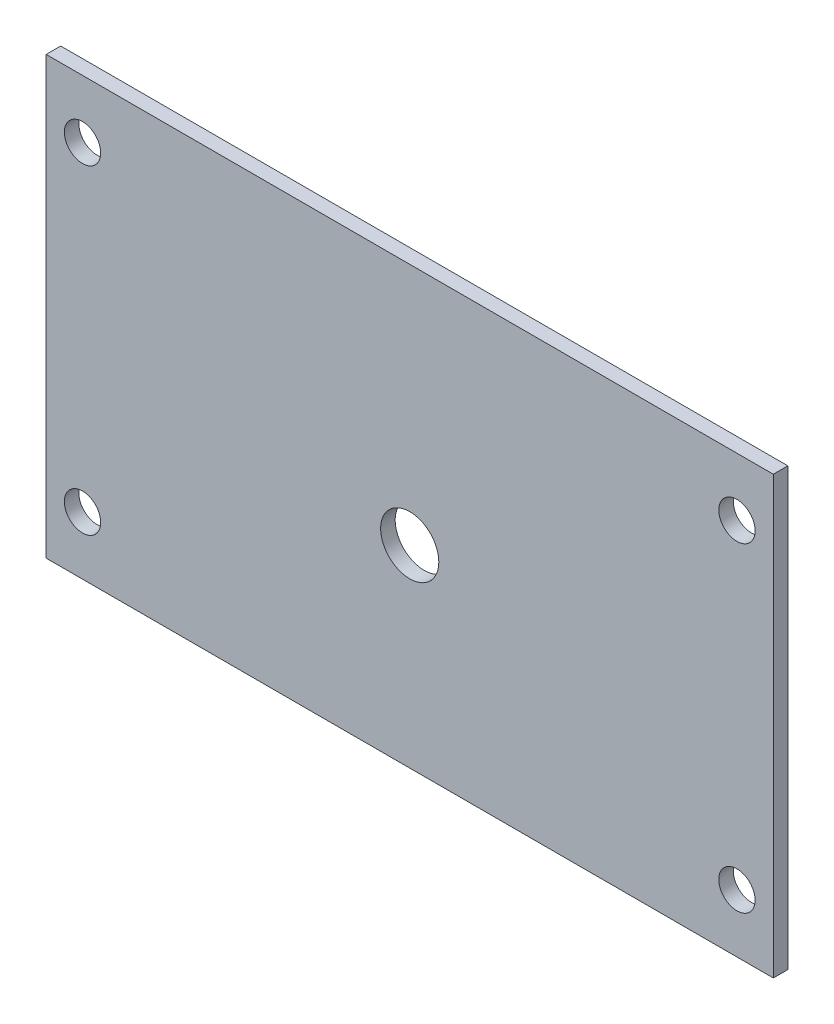
SolidWorks part; units mm, degrees
ref_plane "Front Plane" through (0, 0, 0) normal (0, 0, 1) x (1, 0, 0)
ref_plane "Top Plane" through (0, 0, 0) normal (0, 1, 0) x (1, 0, 0)
ref_plane "Right Plane" through (0, 0, 0) normal (1, 0, 0) x (0, 0, -1)
sketch "Sketch1" plane through (0, 0, 0) normal (0, 0, 1) x (1, 0, 0)
  line L0 (0, 30) -> (0, -30) construction
  line L1 (-50, -30) -> (50, -30)
  line L2 (-50, -30) -> (-50, 30)
  line L3 (-50, 30) -> (50, 30)
  line L4 (50, -30) -> (50, 30)
  line L5 (-50, -30) -> (50, 30) construction
  line L6 (-50, 30) -> (50, -30) construction
  circle A0 centre (0, -3.4588) radius 4
  circle A1 centre (-45, 22) radius 2.5
  circle A2 centre (-45, -22) radius 2.5
  circle A3 centre (45, -22) radius 2.5
  circle A4 centre (45, 22) radius 2.5
  point P0 (0, 0)
  dimension "D3" = 8
  dimension "D4" = 5
  dimension "D7" = 5
  dimension "D1" = 100
  dimension "D2" = 60
  dimension "D5" = 8
  dimension "D6" = 5
  dimension "D8" = 8
  dimension "D9" = 5
extrude "Boss-Extrude1" add sketch "Sketch1" along normal blind 2
